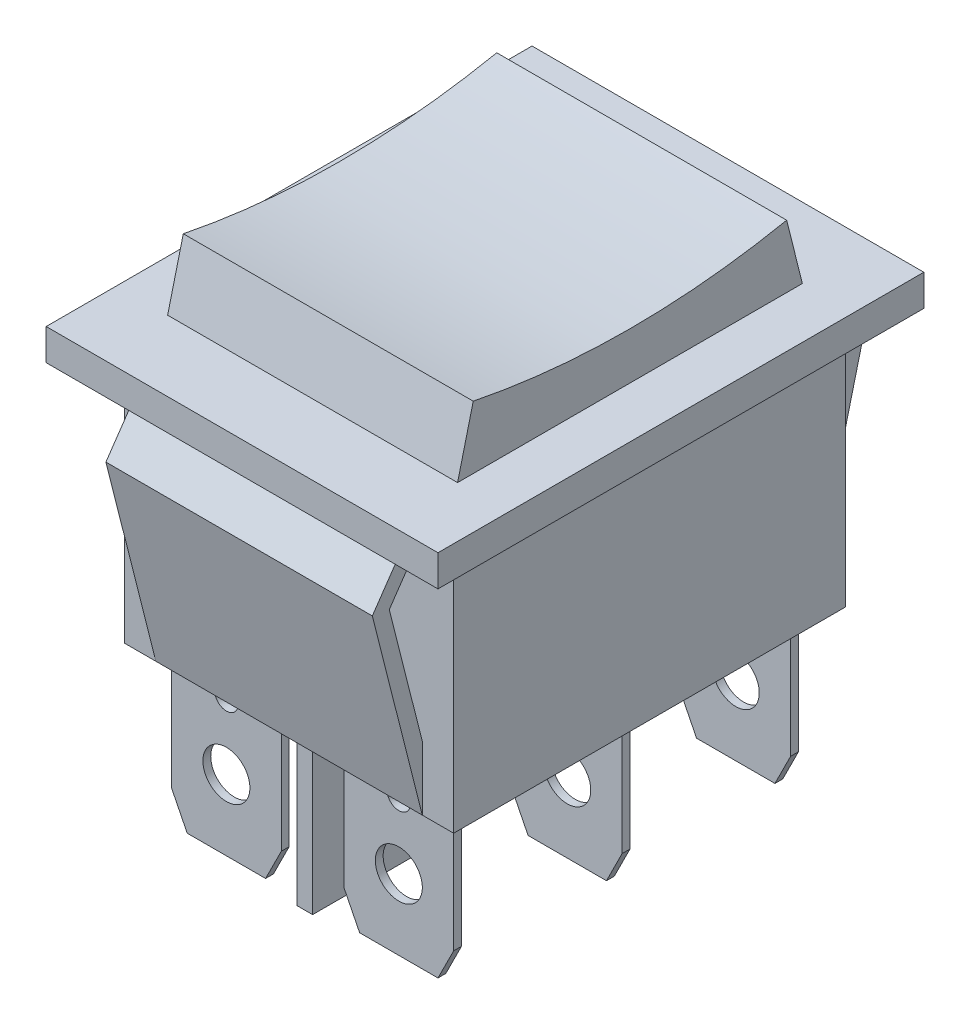
SolidWorks part; units mm, degrees
ref_plane "Спереди" through (0, 0, 0) normal (0, 0, 1) x (1, 0, 0)
ref_plane "Сверху" through (0, 0, 0) normal (0, 1, 0) x (1, 0, 0)
ref_plane "Справа" through (0, 0, 0) normal (1, 0, 0) x (0, 0, -1)
sketch "Эскиз1" plane through (0, 0, 0) normal (0, 1, 0) x (1, 0, 0)
  line L1 (-12.5, 15.5) -> (12.5, 15.5)
  line L2 (-12.5, 15.5) -> (-12.5, -15.5)
  line L3 (-12.5, -15.5) -> (12.5, -15.5)
  line L4 (12.5, 15.5) -> (12.5, -15.5)
  line L5 (-12.5, 15.5) -> (12.5, -15.5) construction
  line L6 (-12.5, -15.5) -> (12.5, 15.5) construction
  point P0 (0, 0)
  dimension "D1" = 25
  dimension "D2" = 31
extrude "Бобышка-Вытянуть1" add sketch "Эскиз1" along normal blind 2
sketch "Эскиз2" plane through (0, 0, 0) normal (0, -1, 0) x (1, 0, 0)
  line L1 (-10.5, 12.5) -> (10.5, 12.5)
  line L2 (-10.5, 12.5) -> (-10.5, -12.5)
  line L3 (-10.5, -12.5) -> (10.5, -12.5)
  line L4 (10.5, 12.5) -> (10.5, -12.5)
  line L5 (-10.5, 12.5) -> (10.5, -12.5) construction
  line L6 (-10.5, -12.5) -> (10.5, 12.5) construction
  point P0 (0, 0)
  dimension "D1" = 25
  dimension "D2" = 21
extrude "Бобышка-Вытянуть2" add sketch "Эскиз2" along normal blind 16
sketch "Эскиз3" plane through (0, 0, 0) normal (1, 0, 0) x (0, 0, -1)
  line L0 (0, -1000) -> (0, 49000) construction
  line L1 (11, 2) -> (-11, 2)
  line L2 (-11, 2) -> (-10, 6)
  line L3 (-15.5, 2) -> (15.5, 2) construction
  line L4 (11, 2) -> (10, 6)
  arc A0 (-10, 6) -> (10, 6) centre (0, 55.5) ccw
  point P7 (0, 5)
  point P8 (0, 0)
  point P11 (0, 0)
  point P13 (0, 2)
  dimension "D1" = 22
  dimension "D2" = 4
  dimension "D3" = 20
  dimension "D4" = 3
extrude "Бобышка-Вытянуть3" add sketch "Эскиз3" along normal mid plane 18.5
sketch "Эскиз4" plane through (0, 0, 0) normal (1, 0, 0) x (0, 0, -1)
  line L0 (-12.5, -16) -> (-15.6889, -3.3972)
  line L1 (-15.6889, -3.3972) -> (-13.4243, -0.1)
  line L2 (-13.4243, -0.1) -> (-12.6, -0.6662)
  line L3 (-12.6, -0.6662) -> (-14.6085, -3.5905)
  line L4 (-14.6085, -3.5905) -> (-11.5306, -15.7547)
  line L5 (-11.5306, -15.7547) -> (-12.5, -16)
  line L10 (0, -1000) -> (0, 49000) construction
  line L11 (14.6085, -3.5905) -> (11.5306, -15.7547)
  line L12 (12.6, -0.6662) -> (14.6085, -3.5905)
  line L13 (13.4243, -0.1) -> (12.6, -0.6662)
  line L14 (15.6889, -3.3972) -> (13.4243, -0.1)
  line L15 (12.5, -16) -> (15.6889, -3.3972)
  line L16 (11.5306, -15.7547) -> (12.5, -16)
  line L17 (-15.5, 0) -> (15.5, 0) construction
  line L18 (-12.5, -16) -> (-12.5, 0) construction
  point P8 (-12.7158, -0.6578)
  point P10 (-13.2943, -0.229)
  point P20 (0, 0)
  point P22 (0, 0)
  dimension "D4" = 0.1
  dimension "D1" = 13
  dimension "D2" = 1
  dimension "D3" = 4
  dimension "D5" = 0.1
extrude "Бобышка-Вытянуть5" add sketch "Эскиз4" along normal mid plane 17
sketch "Эскиз5" plane through (0, -16, 0) normal (0, -1, 0) x (1, 0, 0)
  line L0 (0, -1000) -> (0, 49000) construction
  line L1 (-1000, 0) -> (49000, 0) construction
  line L2 (8.5, 12.5) -> (-8.5, 12.5) construction
  line L3 (-0.5, -11.5) -> (0.5, -11.5)
  line L4 (-0.5, -11.5) -> (-0.5, 11.5)
  line L5 (-0.5, 11.5) -> (0.5, 11.5)
  line L6 (0.5, -11.5) -> (0.5, 11.5)
  line L7 (-0.5, -11.5) -> (0.5, 11.5) construction
  line L8 (-0.5, 11.5) -> (0.5, -11.5) construction
  line L9 (1, -10.5) -> (10, -10.5)
  line L10 (1, 11) -> (10, 11)
  line L11 (1, 11) -> (1, 10.5)
  line L12 (1, 10.5) -> (10, 10.5)
  line L13 (10, 11) -> (10, 10.5)
  line L14 (1, 0.25) -> (10, 0.25)
  line L15 (1, 0.25) -> (1, -0.25)
  line L16 (1, -0.25) -> (10, -0.25)
  line L17 (10, 0.25) -> (10, -0.25)
  line L22 (10, -11) -> (10, -10.5)
  line L23 (1, -11) -> (10, -11)
  line L24 (1, -11) -> (1, -10.5)
  line L25 (-1, -11) -> (-1, -10.5)
  line L26 (-1, -11) -> (-10, -11)
  line L27 (-10, -11) -> (-10, -10.5)
  line L28 (-1, -10.5) -> (-10, -10.5)
  line L29 (-1, -0.25) -> (-10, -0.25)
  line L30 (-10, 0.25) -> (-10, -0.25)
  line L31 (-1, 0.25) -> (-10, 0.25)
  line L32 (-1, 0.25) -> (-1, -0.25)
  line L33 (-1, 10.5) -> (-10, 10.5)
  line L34 (-10, 11) -> (-10, 10.5)
  line L35 (-1, 11) -> (-10, 11)
  line L36 (-1, 11) -> (-1, 10.5)
  point P4 (0, 0)
  point P20 (1, 0)
  dimension "D1" = 1
  dimension "D2" = 1
  dimension "D3" = 0.5
  dimension "D4" = 0.5
  dimension "D5" = 0.5
  dimension "D6" = 9
extrude "Бобышка-Вытянуть6" add sketch "Эскиз5" along normal blind 10
sketch "Эскиз6" plane through (0, 0, -11) normal (0, 0, -1) x (-1, 0, 0)
  line L0 (-5.5, -26) -> (-5.5, -16) construction
  line L1 (-1, -26) -> (-10, -26) construction
  line L2 (-1, -16) -> (-10, -16) construction
  line L3 (-10.25, -16.5) -> (-9, -16.5)
  line L4 (-9, -16.5) -> (-9, -24)
  line L5 (-9, -24) -> (-8, -26)
  line L6 (-8, -26) -> (-8, -27.8075)
  line L7 (-8, -27.8075) -> (-10.25, -27.8075)
  line L8 (-10.25, -27.8075) -> (-10.25, -16.5)
  line L9 (-10, -26) -> (-10, -16) construction
  line L10 (-3, -27.8075) -> (-0.75, -27.8075)
  line L11 (-3, -26) -> (-3, -27.8075)
  line L12 (-2, -24) -> (-3, -26)
  line L13 (-2, -16.5) -> (-2, -24)
  line L14 (-0.75, -16.5) -> (-2, -16.5)
  line L15 (-0.75, -27.8075) -> (-0.75, -16.5)
  line L16 (0, -1026) -> (0, 48974) construction
  line L17 (0.5, -26) -> (-0.5, -26) construction
  line L18 (3, -26) -> (3, -27.8075)
  line L19 (2, -24) -> (3, -26)
  line L20 (2, -16.5) -> (2, -24)
  line L21 (0.75, -16.5) -> (2, -16.5)
  line L22 (0.75, -27.8075) -> (0.75, -16.5)
  line L23 (3, -27.8075) -> (0.75, -27.8075)
  line L24 (8, -27.8075) -> (10.25, -27.8075)
  line L25 (8, -26) -> (8, -27.8075)
  line L26 (9, -24) -> (8, -26)
  line L27 (9, -16.5) -> (9, -24)
  line L28 (10.25, -16.5) -> (9, -16.5)
  line L29 (10.25, -27.8075) -> (10.25, -16.5)
  circle A0 centre (-5.5, -21.5) radius 1.5
  circle A1 centre (-5.5, -17.25) radius 0.75
  circle A2 centre (5.5, -17.25) radius 0.75
  circle A3 centre (5.5, -21.5) radius 1.5
  point P35 (0, -26)
  dimension "D1" = 3
  dimension "D2" = 1.5
  dimension "D4" = 1
  dimension "D5" = 2
  dimension "D3" = 3
  dimension "D6" = 11.3075
  dimension "D7" = 0.25
  dimension "D8" = 2
  dimension "D9" = 1
extrude "Вырез-Вытянуть1" cut sketch "Эскиз6" against normal through all
